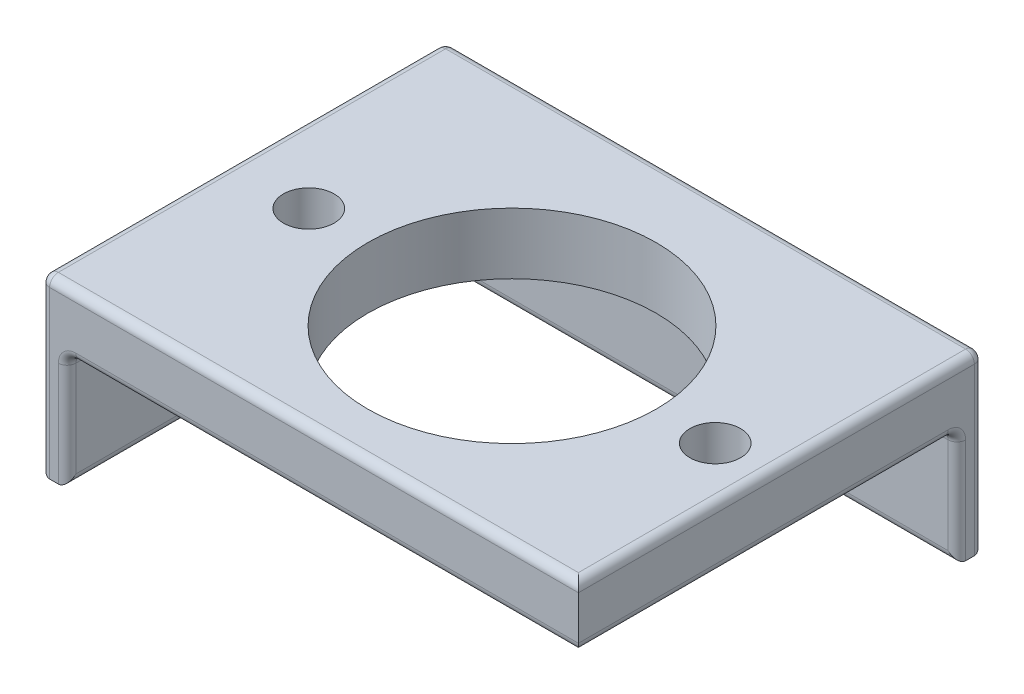
SolidWorks part; units mm, degrees
ref_plane "Front Plane" through (0, 0, 0) normal (0, 0, 1) x (1, 0, 0)
ref_plane "Top Plane" through (0, 0, 0) normal (0, 1, 0) x (1, 0, 0)
ref_plane "Right Plane" through (0, 0, 0) normal (1, 0, 0) x (0, 0, -1)
sketch "Sketch1" plane through (0, 0, 0) normal (0, 1, 0) x (1, 0, 0)
  line L1 (29.25, -21.65) -> (-29.25, -21.65)
  line L2 (29.25, -21.65) -> (29.25, 21.65)
  line L3 (29.25, 21.65) -> (-29.25, 21.65)
  line L4 (-29.25, -21.65) -> (-29.25, 21.65)
  line L5 (29.25, -21.65) -> (-29.25, 21.65) construction
  line L6 (29.25, 21.65) -> (-29.25, -21.65) construction
  circle A0 centre (0, 0) radius 16.5
  point P0 (0, 0)
  dimension "D3" = 33
  dimension "D1" = 58.5
  dimension "D2" = 43.3
extrude "Boss-Extrude1" add sketch "Sketch1" along normal blind 7
sketch "Sketch2" plane through (0, 7, 0) normal (0, 1, 0) x (1, 0, 0)
  line L0 (0, 37.5932) -> (0, -32.3678) construction
  line L1 (-36.9637, 0) -> (42.9309, 0) construction
  point P0 (-23.25, 0)
  point P1 (23.25, 0)
  dimension "D1" = 46.5
hole_wizard "M5 Clearance Hole1" positions "Sketch3" profile "Sketch4" hole size "M5" standard "ANSI Metric" end condition up to next
sketch "Sketch3" plane through (0, 7, 0) normal (0, 1, 0) x (1, 0, 0)
  point P0 (-23.25, 0)
  point P3 (23.25, 0)
sketch "Sketch4" plane through (-23.25, 7, 0) normal (1, 0, 0) x (0, 0, 1)
  line L0 (0, 0) -> (0, 7)
  line L1 (0, 7) -> (2.9, 7)
  line L2 (2.9, 7) -> (2.9, 0)
  line L5 (2.9, 0) -> (0, 0)
  line L11 (0, -6.35) -> (0, 107.95) construction
  dimension "Thru Hole Dia." = 5.8
  dimension "Thru Hole Depth" = 7
sketch "Sketch5" plane through (0, 0, -21.65) normal (0, 0, -1) x (-1, 0, 0)
  line L1 (29.25, 7) -> (-29.25, 7)
  line L2 (29.25, 7) -> (29.25, -12.98)
  line L3 (29.25, -12.98) -> (-29.25, -12.98)
  line L4 (-29.25, 7) -> (-29.25, -12.98)
  dimension "D1" = 19.98
extrude "Boss-Extrude2" add sketch "Sketch5" along normal blind 3
sketch "Sketch6" plane through (-29.25, 0, 0) normal (-1, 0, 0) x (0, 0, 1)
  line L0 (21.65, 7) -> (21.65, 0) construction
  line L1 (-24.65, 7) -> (21.65, 7)
  line L2 (-24.65, 7) -> (-24.65, -12.98)
  line L3 (-24.65, -12.98) -> (21.65, -12.98)
  line L4 (21.65, 7) -> (21.65, -12.98)
  dimension "D1" = 19.98
extrude "Boss-Extrude3" add sketch "Sketch6" along normal blind 3
sketch "Sketch7" plane through (0, 0, -21.65) normal (0, 0, 1) x (1, 0, 0)
  line L0 (-36.8901, -4.79) -> (36.0772, -4.79) construction
  line L1 (29.25, -12.98) -> (-29.25, -12.98) construction
  line L2 (0, 11.6355) -> (0, -17.8563) construction
  point P4 (-17, -4.79)
  point P5 (17, -4.79)
  dimension "D1" = 8.19
  dimension "D2" = 17
sketch "Sketch8" plane through (-29.25, 0, 0) normal (1, 0, 0) x (0, 0, -1)
  line L0 (-23.397, -4.79) -> (34.0807, -4.79) construction
  line L1 (21.65, -12.98) -> (-21.65, -12.98) construction
  line L2 (-21.65, -12.98) -> (-21.65, 0) construction
  line L3 (21.65, 11.6355) -> (21.65, -17.8563) construction
  point P4 (-11.65, -4.79)
  point P5 (11.65, -4.79)
  dimension "D1" = 8.19
  dimension "D2" = 10
  dimension "D3" = 10
hole_wizard "M5 Clearance Hole2" positions "Sketch9" profile "Sketch10" hole size "M5" standard "ANSI Metric" end condition up to next
sketch "Sketch9" plane through (0, 0, -21.65) normal (0, 0, 1) x (1, 0, 0)
  point P0 (-17, -4.79)
  point P3 (17, -4.79)
sketch "Sketch10" plane through (-17, -4.79, -21.65) normal (1, 0, 0) x (0, -1, 0)
  line L0 (0, 0) -> (0, 3)
  line L1 (0, 3) -> (2.75, 3)
  line L2 (2.75, 3) -> (2.75, 0)
  line L5 (2.75, 0) -> (0, 0)
  line L11 (0, -6.35) -> (0, 107.95) construction
  dimension "Thru Hole Dia." = 5.5
  dimension "Thru Hole Depth" = 3
hole_wizard "M5 Clearance Hole3" positions "Sketch11" profile "Sketch12" hole size "M5" standard "ANSI Metric" end condition up to next
sketch "Sketch11" plane through (-29.25, 0, 0) normal (1, 0, 0) x (0, 0, -1)
  point P0 (-11.65, -4.79)
  point P3 (11.65, -4.79)
sketch "Sketch12" plane through (-29.25, -4.79, 11.65) normal (0, 1, 0) x (0, 0, -1)
  line L0 (0, 0) -> (0, 3)
  line L1 (0, 3) -> (2.75, 3)
  line L2 (2.75, 3) -> (2.75, 0)
  line L5 (2.75, 0) -> (0, 0)
  line L11 (0, -6.35) -> (0, 107.95) construction
  dimension "Thru Hole Dia." = 5.5
  dimension "Thru Hole Depth" = 3
fillet "Fillet1" radius 1 9 edges at (29.25, 0, 0) (0, 0, 21.65) (29.25, -6.49, -21.65) (-29.25, -6.49, 21.65) (-29.25, 0, 0) (0, 0, -21.65) (-29.25, -6.49, -21.65) (0, -12.98, -21.65) (-29.25, -12.98, 0)
fillet "Fillet2" radius 1 9 edges at (29.25, -2.99, -24.65) (-1.5, 7, -24.65) (-32.25, -2.99, -24.65) (-1.5, -12.98, -24.65) (-32.25, 7, -1.5) (-32.25, -2.99, 21.65) (-32.25, -12.98, -1.5) (-1.5, 7, 21.65) (29.25, 7, -1.5)
